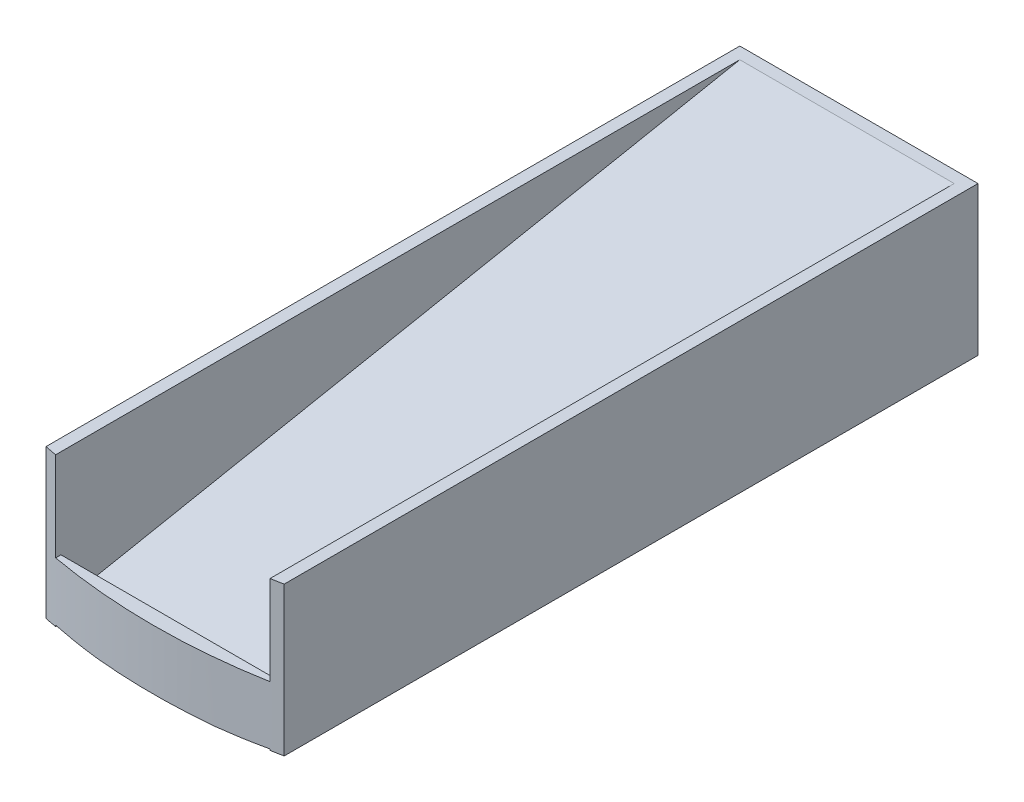
SolidWorks part; units mm, degrees
ref_plane "Front Plane" through (0, 0, 0) normal (0, 0, 1) x (1, 0, 0)
ref_plane "Top Plane" through (0, 0, 0) normal (0, 1, 0) x (1, 0, 0)
ref_plane "Right Plane" through (0, 0, 0) normal (1, 0, 0) x (0, 0, -1)
sketch "Sketch1" plane through (0, 0, 0) normal (0, 0, 1) x (1, 0, 0)
  line L1 (-20, 12.5) -> (20, 12.5)
  line L2 (-20, 12.5) -> (-20, -12.5)
  line L3 (-20, -12.5) -> (20, -12.5)
  line L4 (20, 12.5) -> (20, -12.5)
  line L5 (-20, 12.5) -> (20, -12.5) construction
  line L6 (-20, -12.5) -> (20, 12.5) construction
  point P0 (0, 0)
  dimension "D1" = 40
  dimension "D2" = 25
extrude "Boss-Extrude1" add sketch "Sketch1" along normal mid plane 120
sketch "Sketch4" plane through (0, 0, 0) normal (1, 0, 0) x (0, 0, -1)
  line L0 (-60, -10.5) -> (58, 12.5)
  line L1 (-60, -12.5) -> (-60, 12.5) construction
  line L3 (-60, 12.5) -> (60, 12.5) construction
  line L4 (58, 12.5) -> (-60, 12.5)
  line L5 (-60, 12.5) -> (-60, -10.5)
  line L6 (-60, -12.5) -> (60, -12.5) construction
  line L7 (-58, -12.5) -> (60, 10.5)
  line L8 (60, -12.5) -> (60, 12.5) construction
  line L9 (60, 10.5) -> (60, -12.5)
  line L10 (60, -12.5) -> (-58, -12.5)
  dimension "D1" = 2
  dimension "D2" = 2
extrude "Cut-Extrude3" cut sketch "Sketch4" against normal mid plane 36
sketch "Sketch6" plane through (0, 0, 60) normal (0, 0, 1) x (1, 0, 0)
  line L0 (18, 12.5) -> (18, -10.5) construction
  line L1 (-18, -10.5) -> (18, -10.5)
  line L2 (-18, -10.5) -> (-18, -2.5)
  line L3 (-18, -2.5) -> (18, -2.5)
  line L4 (18, -10.5) -> (18, -2.5)
  dimension "D1" = 8
extrude "Boss-Extrude2" add sketch "Sketch6" against normal blind 4
sketch "Sketch7" plane through (0, 12.5, 0) normal (0, 1, 0) x (1, 0, 0)
  line L1 (20, 60) -> (-20, 60) construction
  circle A0 centre (0, 43) radius 101.5
  circle A1 centre (0, 43) radius 500
  point P2 (0, 60)
  point P3 (0, 28.9099)
  dimension "D1" = 203
  dimension "D2" = 1000
  dimension "D3" = 17
extrude "Cut-Extrude4" cut sketch "Sketch7" against normal through all
